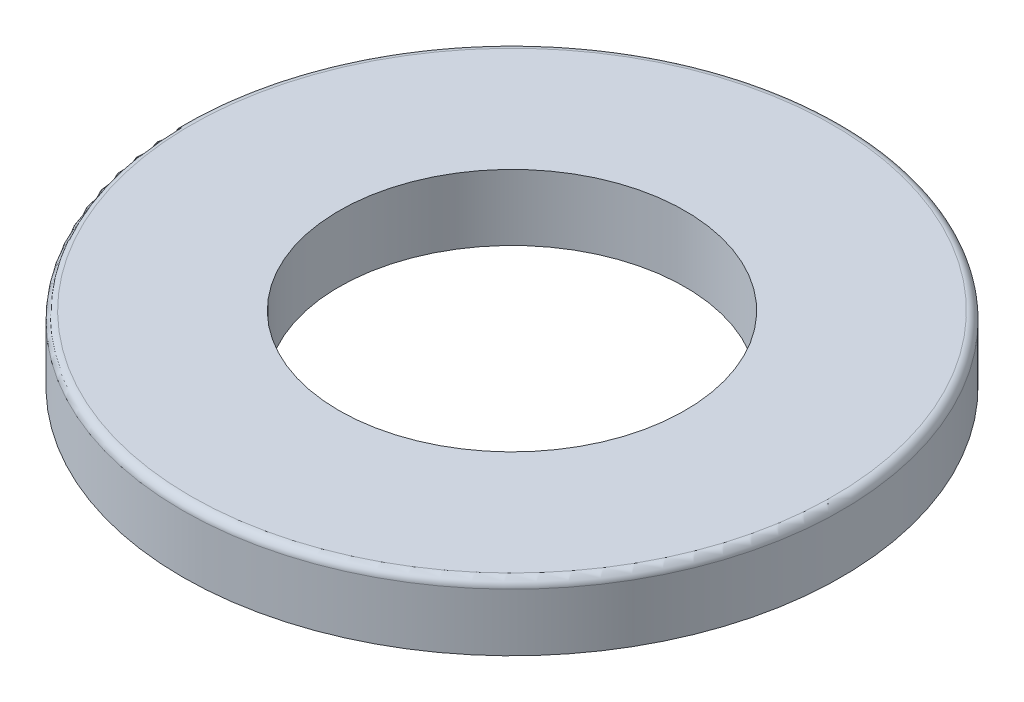
SolidWorks part; units mm, degrees
ref_plane "Front Plane" through (0, 0, 0) normal (0, 0, 1) x (1, 0, 0)
ref_plane "Top Plane" through (0, 0, 0) normal (0, 1, 0) x (1, 0, 0)
ref_plane "Right Plane" through (0, 0, 0) normal (1, 0, 0) x (0, 0, -1)
sketch "Sketch1" plane through (0, 0, 0) normal (0, 1, 0) x (1, 0, 0)
  circle A0 centre (0, 0) radius 4.2
  circle A1 centre (0, 0) radius 8
  dimension "D1" = 16
  dimension "D2" = 8.4
extrude "Boss-Extrude1" add sketch "Sketch1" along normal blind 1.6
fillet "Fillet1" radius 0.2 1 edges at (0, 1.6, 8)
